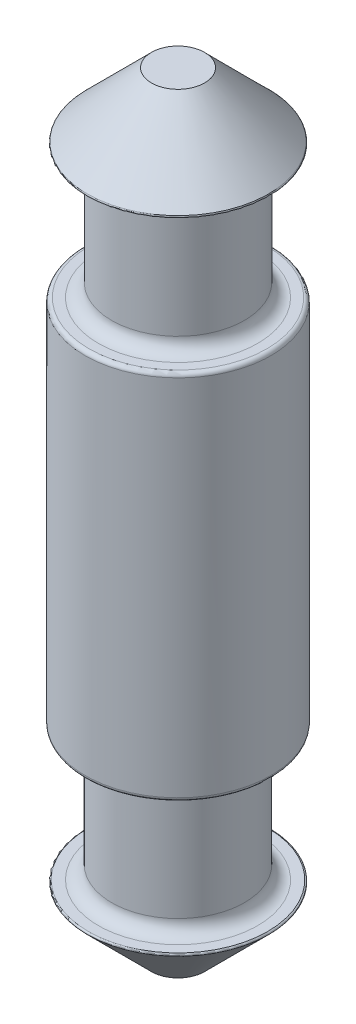
SolidWorks part; units mm, degrees
ref_plane "Front" through (0, 0, 0) normal (0, 0, 1) x (1, 0, 0)
ref_plane "Top" through (0, 0, 0) normal (0, 1, 0) x (1, 0, 0)
ref_plane "Right" through (0, 0, 0) normal (1, 0, 0) x (0, 0, -1)
sketch "Sketch1" plane through (0, 0, 0) normal (0, 1, 0) x (1, 0, 0)
  circle A0 centre (0, 0) radius 7
  dimension "D1" = 14
extrude "Boss-Extrude1" add sketch "Sketch1" along normal blind 14
sketch "Sketch2" plane through (0, 14, 0) normal (0, 1, 0) x (1, 0, 0)
  circle A0 centre (0, 0) radius 5
  dimension "D1" = 10
extrude "Boss-Extrude2" add sketch "Sketch2" along normal blind 10
sketch "Sketch3" plane through (0, 0, 0) normal (0, -1, 0) x (1, 0, 0)
  circle A0 centre (0, 0) radius 5
  dimension "D1" = 10
sketch "Sketch4" plane through (0, 24, 0) normal (0, 1, 0) x (1, 0, 0)
  circle A0 centre (0, 0) radius 7
  dimension "D1" = 14
extrude "Boss-Extrude4" add sketch "Sketch4" along normal blind 5 draft 45
fillet "Fillet1" radius 0.1 1 edges at (0, 24, 7)
mirror "Mirror1" about plane through (0, 0, 0) normal (0, 1, 0) of bodies 118
fillet "Fillet3" radius 0.3 2 edges at (0, -14, 7) (0, 14, 7)
fillet "Fillet4" radius 1 2 edges at (0, -24, 5) (0, 24, 5)
fillet "Fillet5" radius 1 2 edges at (0, 14, 5) (0, -14, 5)
